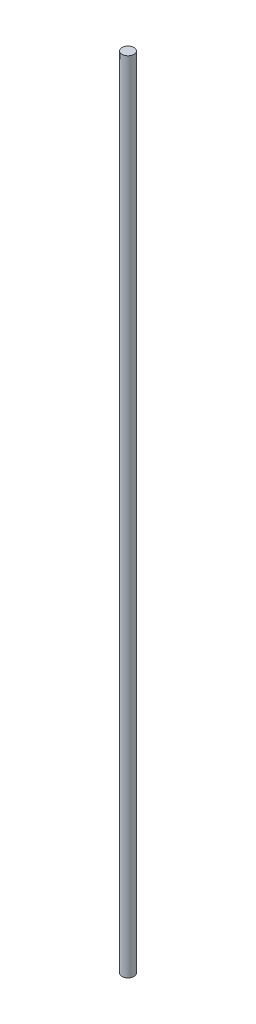
SolidWorks part; units mm, degrees
material "Nylon 101"
ref_plane "Front Plane" through (0, 0, 0) normal (0, 0, 1) x (1, 0, 0)
ref_plane "Top Plane" through (0, 0, 0) normal (0, 1, 0) x (1, 0, 0)
ref_plane "Right Plane" through (0, 0, 0) normal (1, 0, 0) x (0, 0, -1)
sketch "Sketch1" plane through (0, 0, 0) normal (0, 1, 0) x (1, 0, 0)
  circle A0 centre (0, 0) radius 0.375
  dimension "D1" = 0.75
extrude "Boss-Extrude1" add sketch "Sketch1" along normal blind 50
